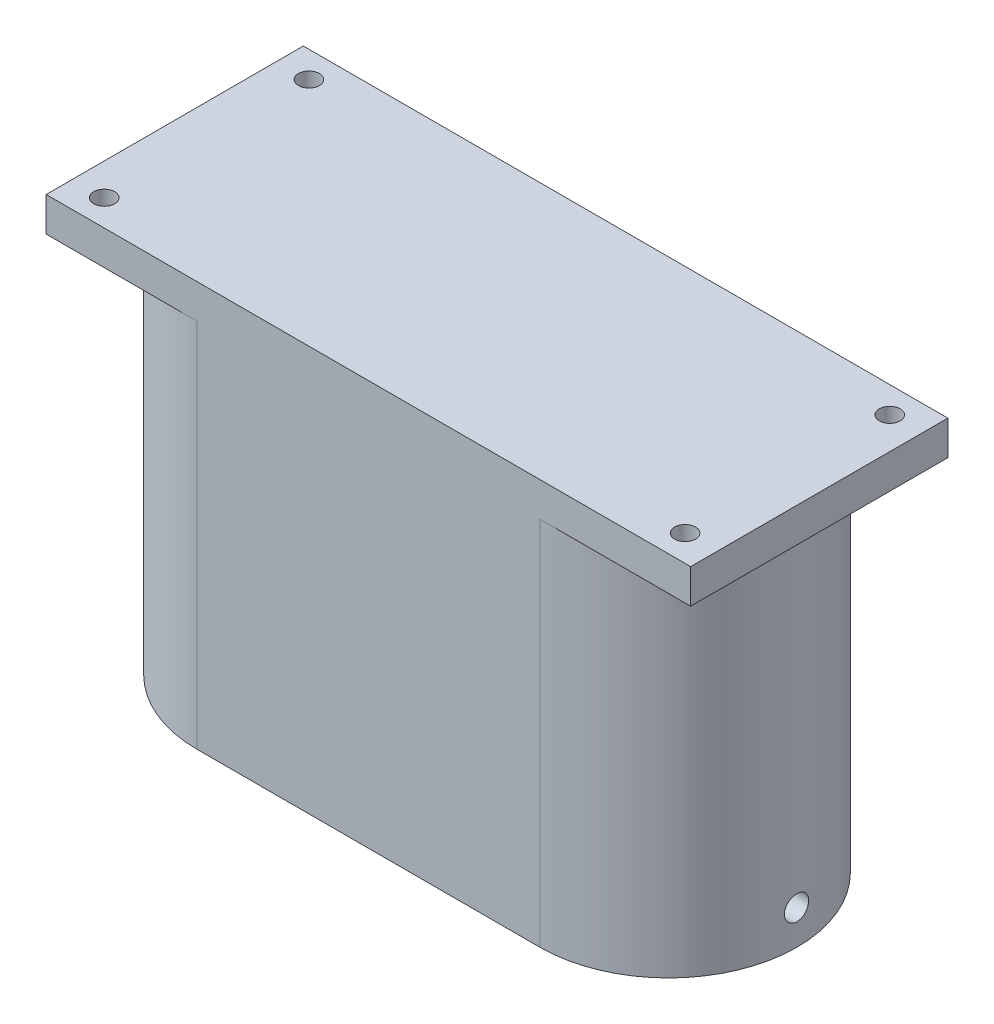
SolidWorks part; units mm, degrees
ref_plane "Front Plane" through (0, 0, 0) normal (0, 0, 1) x (1, 0, 0)
ref_plane "Top Plane" through (0, 0, 0) normal (0, 1, 0) x (1, 0, 0)
ref_plane "Right Plane" through (0, 0, 0) normal (1, 0, 0) x (0, 0, -1)
sketch "Sketch1" plane through (0, 0, 0) normal (0, 1, 0) x (1, 0, 0)
  line L1 (-25.4, -19.05) -> (25.4, -19.05)
  line L2 (-25.4, 19.05) -> (25.4, 19.05)
  line L4 (-25.4, -19.05) -> (25.4, 19.05) construction
  line L5 (-25.4, 19.05) -> (25.4, -19.05) construction
  line L6 (-44.45, 0) -> (44.45, 0) construction
  line L7 (-25.4, -13.97) -> (25.4, -13.97)
  line L8 (-25.4, 13.97) -> (25.4, 13.97)
  arc A0 (-25.4, 19.05) -> (-25.4, -19.05) centre (-25.4, 0) ccw
  arc A2 (25.4, -19.05) -> (25.4, 19.05) centre (25.4, 0) ccw
  arc A3 (-25.4, 13.97) -> (-25.4, -13.97) centre (-25.4, 0) ccw
  arc A4 (25.4, -13.97) -> (25.4, 13.97) centre (25.4, 0) ccw
  point P1 (0, 0)
  point P16 (39.37, 0)
  point P17 (44.45, 0)
  point P18 (0, 0)
  point P19 (-39.37, 0)
  dimension "D1" = 78.74
  dimension "D2" = 27.94
  dimension "D3" = 5.08
extrude "Boss-Extrude1" add sketch "Sketch1" along normal blind 60
sketch "Sketch2" plane through (0, 60, 0) normal (0, 1, 0) x (1, 0, 0)
  line L0 (-47.7372, -19.05) -> (-47.7372, 19.05)
  line L1 (-47.7372, -19.05) -> (47.7372, -19.05)
  line L2 (-47.7372, 19.05) -> (47.7372, 19.05)
  line L3 (47.7372, -19.05) -> (47.7372, 19.05)
  line L4 (-47.7372, -19.05) -> (47.7372, 19.05) construction
  line L5 (-47.7372, 19.05) -> (47.7372, -19.05) construction
  line L6 (0, 0) -> (47.7372, 0) construction
  line L7 (0, 0) -> (0, 19.05) construction
  circle A0 centre (43.0197, 15.1621) radius 1.55
  circle A3 centre (43.0197, -15.1621) radius 1.55
  circle A4 centre (-43.0197, -15.1621) radius 1.55
  circle A5 centre (-43.0197, 15.1621) radius 1.55
  point P1 (0, 0)
  point P3 (43.0197, -15.1621)
  point P17 (49.3079, 12.9215)
  dimension "D1" = 3.1
extrude "Boss-Extrude2" add sketch "Sketch2" against normal blind 5.08
sketch "Sketch4" plane through (0, 0, 0) normal (1, 0, 0) x (0, 0, -1)
  line L0 (0, 0) -> (0, 5.08) construction
  circle A0 centre (0, 5.08) radius 1.8
  dimension "D1" = 3.6
  dimension "D2" = 5.08
extrude "Cut-Extrude1" cut sketch "Sketch4" against normal blind 107.696 and the other way blind 96.52
